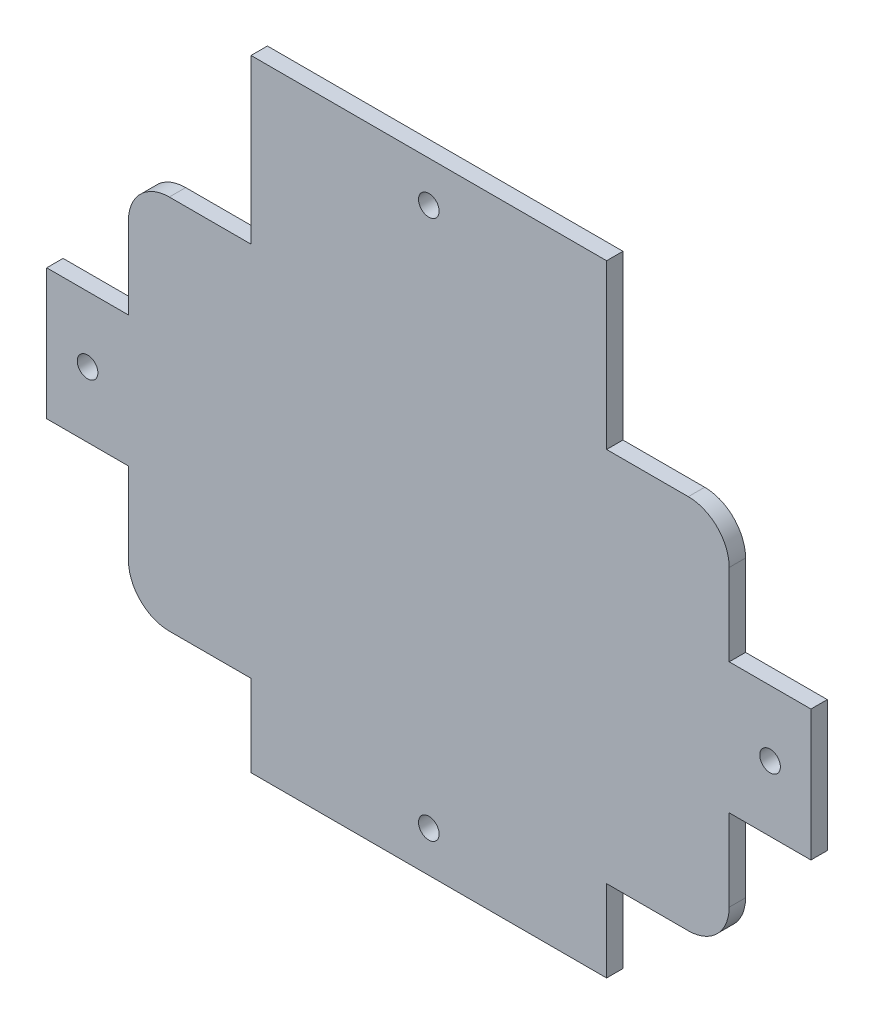
SolidWorks part; units mm, degrees
ref_plane "Front Plane" through (0, 0, 0) normal (0, 0, 1) x (1, 0, 0)
ref_plane "Top Plane" through (0, 0, 0) normal (0, 1, 0) x (1, 0, 0)
ref_plane "Right Plane" through (0, 0, 0) normal (1, 0, 0) x (0, 0, -1)
sketch "Sketch1" plane through (0, 0, 0) normal (0, 0, 1) x (1, 0, 0)
  line L0 (0, 76) -> (0, 86) construction
  line L1 (-43.5, 86) -> (-43.5, 46)
  line L2 (-43.5, 46) -> (-63.5, 46)
  line L3 (-73.5, 36) -> (-73.5, 16)
  line L4 (-73.5, 16) -> (-93.5, 16)
  line L5 (-93.5, 16) -> (-93.5, -16)
  line L6 (-93.5, 0) -> (-83.5, 0) construction
  line L7 (-93.5, -16) -> (-73.5, -16)
  line L8 (-73.5, -16) -> (-73.5, -36)
  line L9 (-63.5, -46) -> (-43.5, -46)
  line L10 (-43.5, -46) -> (-43.5, -66)
  line L11 (-43.5, -66) -> (43.5, -66)
  line L12 (43.5, -66) -> (43.5, -46)
  line L13 (43.5, -46) -> (63.5, -46)
  line L14 (73.5, -36) -> (73.5, -16)
  line L15 (73.5, -16) -> (93.5, -16)
  line L16 (83.5, 0) -> (93.5, 0) construction
  line L17 (93.5, -16) -> (93.5, 16)
  line L18 (93.5, 16) -> (73.5, 16)
  line L19 (0, -66) -> (0, -56) construction
  line L20 (-83.5, 0) -> (0, 0) construction
  line L21 (73.5, 16) -> (73.5, 36)
  line L22 (63.5, 46) -> (43.5, 46)
  line L23 (43.5, 46) -> (43.5, 86)
  line L24 (43.5, 86) -> (-43.5, 86)
  line L25 (0, 0) -> (0, 76) construction
  arc A0 (73.5, 36) -> (63.5, 46) centre (63.5, 36) ccw
  arc A1 (63.5, -46) -> (73.5, -36) centre (63.5, -36) ccw
  arc A2 (-73.5, -36) -> (-63.5, -46) centre (-63.5, -36) ccw
  arc A3 (-63.5, 46) -> (-73.5, 36) centre (-63.5, 36) ccw
  circle A4 centre (0, 76) radius 2.525
  circle A5 centre (-83.5, 0) radius 2.525
  circle A6 centre (83.5, 0) radius 2.525
  circle A7 centre (0, -56) radius 2.525
  point P43 (73.5, 46)
  dimension "D1" = 10
  dimension "D3" = 5.05
  dimension "D8" = 87
  dimension "D10" = 20
  dimension "D13" = 20
  dimension "D2" = 40
  dimension "D4" = 10
  dimension "D5" = 10
  dimension "D6" = 10
  dimension "D7" = 10
  dimension "D9" = 32
  dimension "D11" = 20
  dimension "D12" = 20
extrude "Boss-Extrude1" add sketch "Sketch1" along normal blind 4
